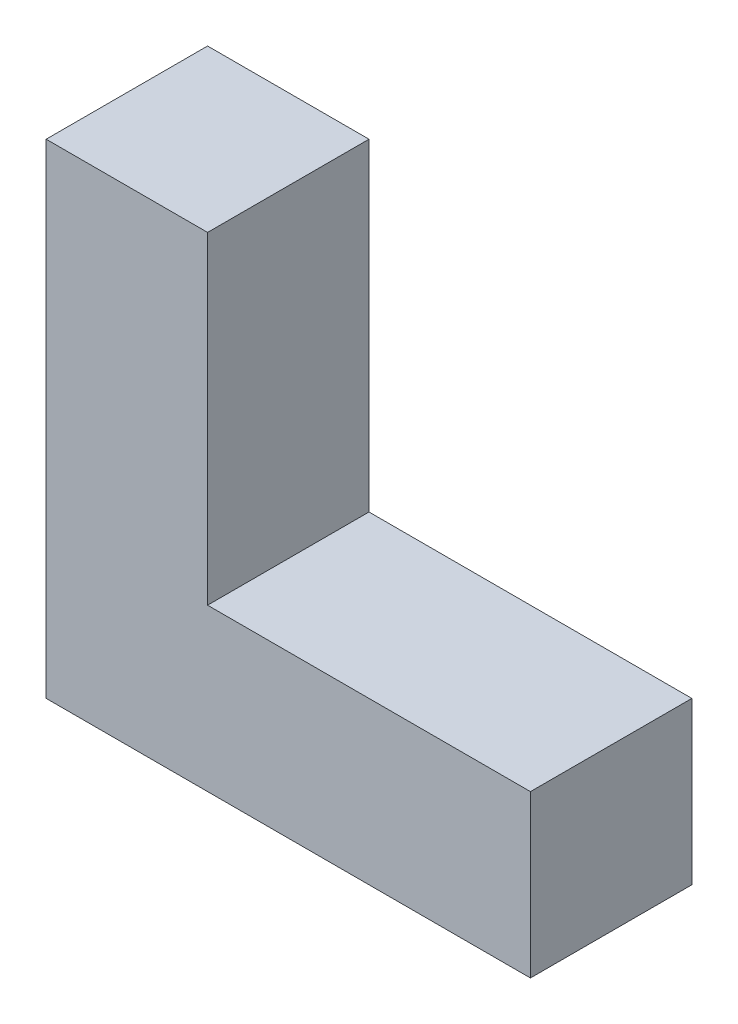
SolidWorks part; units mm, degrees
ref_plane "Front Plane" through (0, 0, 0) normal (0, 0, 1) x (1, 0, 0)
ref_plane "Top Plane" through (0, 0, 0) normal (0, 1, 0) x (1, 0, 0)
ref_plane "Right Plane" through (0, 0, 0) normal (1, 0, 0) x (0, 0, -1)
sketch "Sketch1" plane through (0, 0, 0) normal (0, 0, 1) x (1, 0, 0)
  line L44 (76.2, 0) -> (76.2, 25.4)
  line L45 (76.2, 25.4) -> (25.4, 25.4)
  line L46 (25.4, 25.4) -> (25.4, 76.2)
  line L47 (25.4, 76.2) -> (0, 76.2)
  line L48 (0, 76.2) -> (0, 0)
  line L49 (0, 0) -> (76.2, 0)
extrude "Boss-Extrude1" add sketch "Sketch1" along normal blind 25.4
